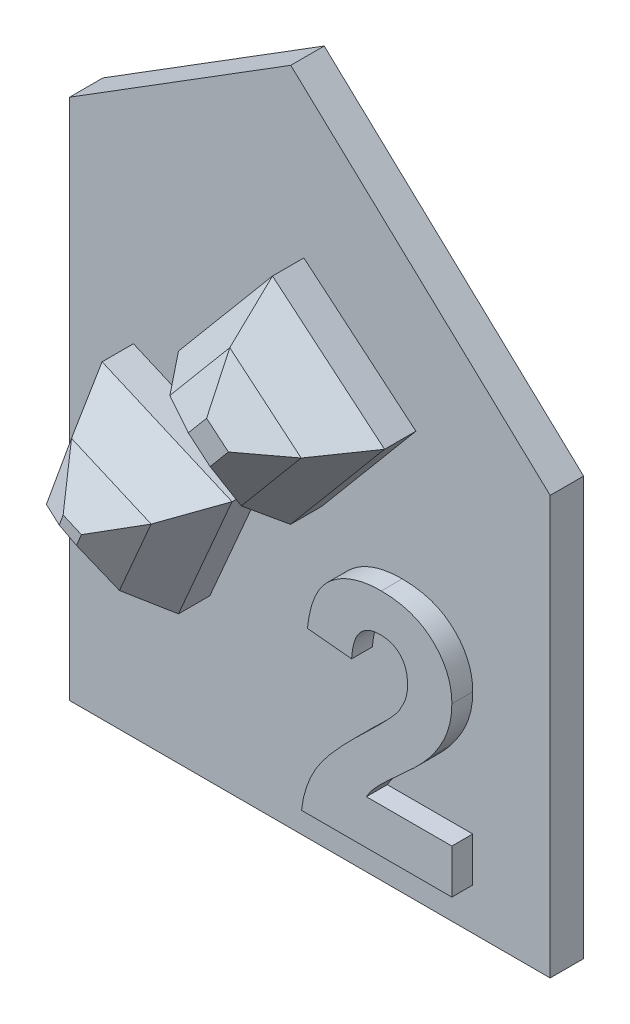
SolidWorks part; units mm, degrees
ref_plane "Přední rovina" through (0, 0, 0) normal (0, 0, 1) x (1, 0, 0)
ref_plane "Horní rovina" through (0, 0, 0) normal (0, 1, 0) x (1, 0, 0)
ref_plane "Pravá rovina" through (0, 0, 0) normal (1, 0, 0) x (0, 0, -1)
sketch "Skica1" plane through (0, 0, 0) normal (0, 0, 1) x (1, 0, 0)
  line L0 (-66.5051, 0) -> (66.5051, 0) construction
  line L1 (0, 0) -> (0, 20)
  line L2 (0, 20) -> (-12.4128, 31.6156)
  line L3 (-12.4128, 31.6156) -> (-23, 25)
  line L4 (-23, 25) -> (-23, 0)
  line L5 (-23, 0) -> (0, 0)
  dimension "D1" = 23
  dimension "D2" = 25
  dimension "D3" = 20
  dimension "D4" = 17
  dimension "D5" = 122
extrude "Přidat vysunutím5" add sketch "Skica1" along normal blind 1.6
sketch "Skica2" plane through (0, 0, 1.6) normal (0, 0, 1) x (1, 0, 0)
  line L1 (-23, 25) -> (-23, 0) construction
  line L2 (0, 0) -> (0, 20) construction
  line L3 (-3, 0) -> (-3, 22.8073) construction
  line L4 (-23, 0) -> (0, 0) construction
  line L5 (0, 20) -> (-12.4128, 31.6156) construction
  line L6 (-23, 2) -> (-3, 2) construction
  text T1 "2" font "Arial" height 11
  dimension "D2" = 3
  dimension "D3" = 2
extrude "Přidat vysunutím6" add sketch "Skica2" along normal blind 1
sketch "Skica3" plane through (0, 0, 1.6) normal (0, 0, 1) x (1, 0, 0)
  line L0 (-23, -0.3065) -> (-3.339, 23.1246) construction
  line L1 (-23, 25) -> (-23, 0) construction
  line L2 (0, 20) -> (-12.4128, 31.6156) construction
  line L3 (0, 0) -> (0, 20) construction
  line L4 (-23, 0) -> (0, 0) construction
  line L5 (-10.9239, 14.0853) -> (-6.4244, 19.4476)
  line L6 (-6.4244, 19.4476) -> (-11.7867, 23.9471)
  line L7 (-11.7867, 23.9471) -> (-16.2862, 18.5848)
  line L8 (-16.2862, 18.5848) -> (-10.9239, 14.0853)
  line L9 (-23, 11.1946) -> (-16.2862, 7.6947) construction
  line L10 (-16.2862, 7.6947) -> (-13.7227, 13.627)
  line L11 (-13.7227, 13.627) -> (-19.9408, 16.314)
  line L12 (-19.9408, 16.314) -> (-21.9762, 10.6609)
  line L13 (-21.9762, 10.6609) -> (-16.2862, 7.6947)
  dimension "D1" = 3.339
  dimension "D2" = 50
  dimension "D3" = 7
  dimension "D4" = 7
  dimension "D5" = 4.8
  dimension "D6" = 11.1946
  dimension "D7" = 10.2119
  dimension "D8" = 6.0084
  dimension "D9" = 6.7738
  dimension "D10" = 5.9323
  dimension "D11" = 1.1441
extrude "Přidat vysunutím7" add sketch "Skica3" along normal blind 5
chamfer "Zkosení1" distance 3.5 angle 30 8 edges at (-19.1312, 9.1778, 6.6) (-20.9585, 13.4874, 6.6) (-16.8318, 14.9705, 6.6) (-15.0045, 10.6609, 6.6) (-8.6741, 16.7664, 6.6) (-13.6051, 16.335, 6.6) (-14.0365, 21.2659, 6.6) (-9.1055, 21.6973, 6.6)
chamfer "Zkosení2" distance 1.5 angle 20 8 edges at (-12.3062, 17.883, 6.6) (-12.4885, 19.967, 6.6) (-10.4044, 20.1494, 6.6) (-10.2221, 18.0653, 6.6) (-16.8292, 11.5324, 6.6) (-18.3781, 11.064, 6.6) (-19.1226, 12.6214, 6.6) (-17.5737, 13.0898, 6.6)
